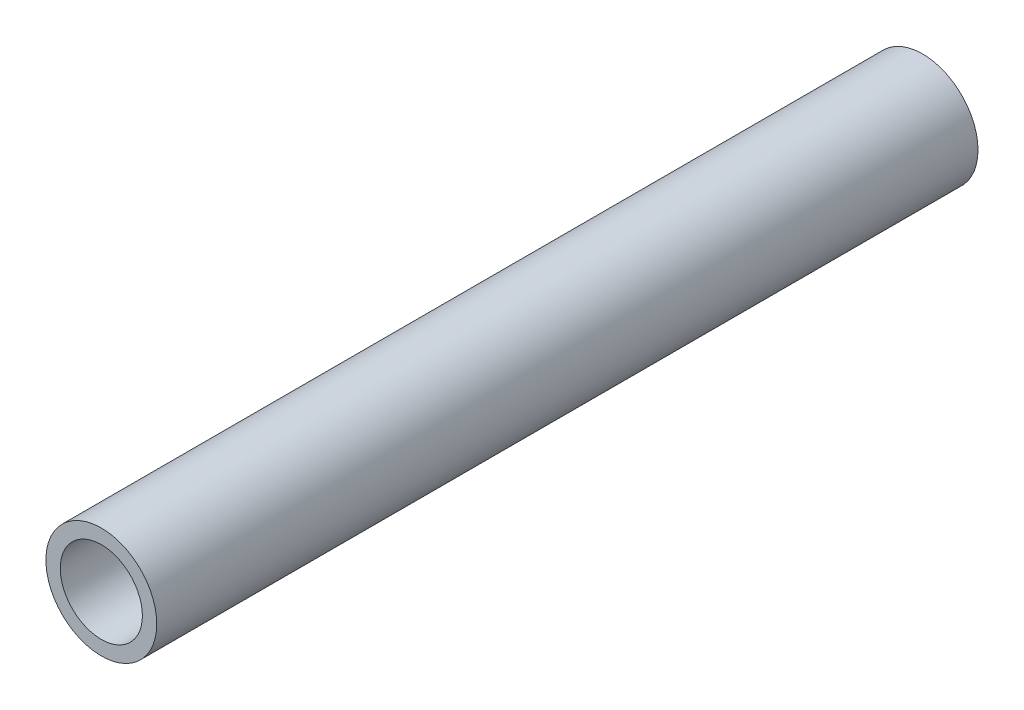
SolidWorks part; units mm, degrees
material "ABS"
ref_plane "Front Plane" through (0, 0, 0) normal (0, 0, 1) x (1, 0, 0)
ref_plane "Top Plane" through (0, 0, 0) normal (0, 1, 0) x (1, 0, 0)
ref_plane "Right Plane" through (0, 0, 0) normal (1, 0, 0) x (0, 0, -1)
sketch "Sketch1" plane through (0, 0, 0) normal (0, 0, 1) x (1, 0, 0)
  circle A0 centre (0, 0) radius 1.35
  circle A1 centre (0, 0) radius 1
  dimension "D1" = 2.7
extrude "Boss-Extrude1" add sketch "Sketch1" along normal blind 20
